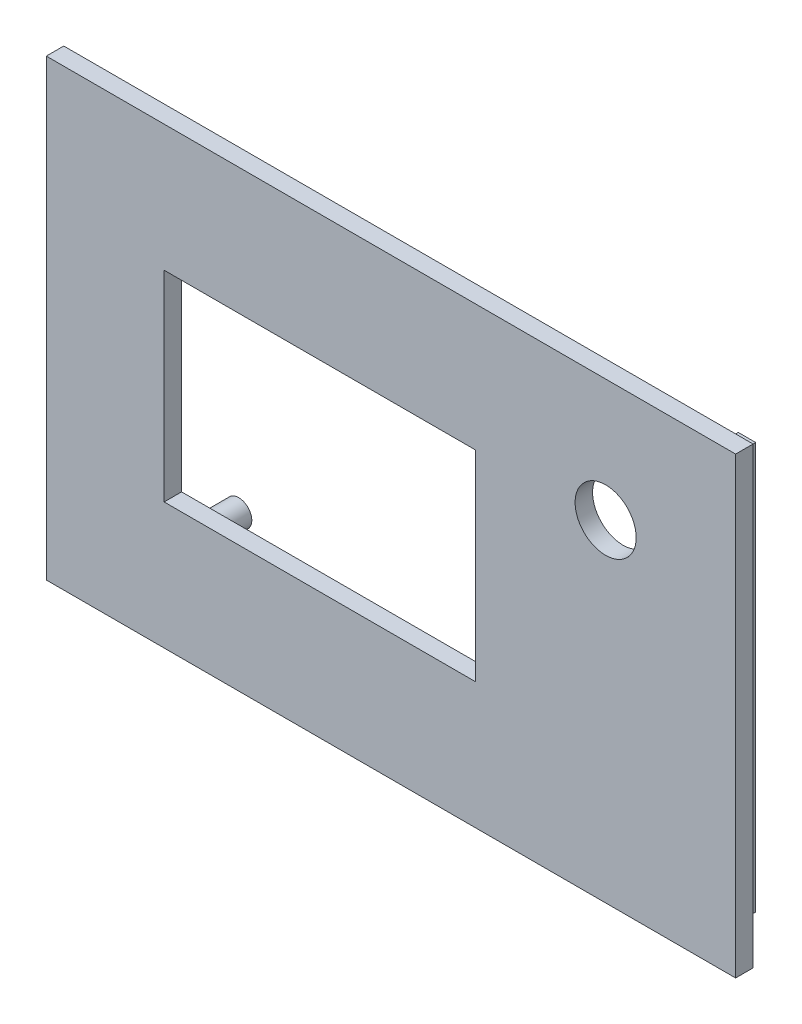
SolidWorks part; units mm, degrees
ref_plane "Ebene vorne" through (0, 0, 0) normal (0, 0, 1) x (1, 0, 0)
ref_plane "Ebene oben" through (0, 0, 0) normal (0, 1, 0) x (1, 0, 0)
ref_plane "Ebene rechts" through (0, 0, 0) normal (1, 0, 0) x (0, 0, -1)
sketch "Skizze10" plane through (0, 0, 0) normal (0, 0, 1) x (1, 0, 0)
  line L1 (-59.4904, -2.4023) -> (19.5096, -2.4023)
  line L2 (-59.4904, -2.4023) -> (-59.4904, -54.4023)
  line L3 (-59.4904, -54.4023) -> (19.5096, -54.4023)
  line L4 (19.5096, -2.4023) -> (19.5096, -54.4023)
  dimension "D1" = 79
  dimension "D2" = 52
extrude "Aufsatz-Linear austragen8" add sketch "Skizze10" along normal blind 2
sketch "Skizze11" plane through (0, 0, 2) normal (0, 0, 1) x (1, 0, 0)
  line L0 (-53.3332, -28.4023) -> (19.5096, -28.4023) construction
  line L1 (-45.987, -16.9023) -> (-10.287, -16.9023)
  line L2 (-45.987, -16.9023) -> (-45.987, -39.9023)
  line L3 (-45.987, -39.9023) -> (-10.287, -39.9023)
  line L4 (-10.287, -16.9023) -> (-10.287, -39.9023)
  line L5 (19.5096, -54.4023) -> (19.5096, -2.4023) construction
  dimension "D1" = 35.7
  dimension "D2" = 23
extrude "Schnitt-Linear austragen3" cut sketch "Skizze11" against normal blind 2
sketch "Skizze13" plane through (0, 0, 2) normal (0, 0, 1) x (1, 0, 0)
  line L0 (4.6113, 9.8264) -> (4.6113, -44.9541) construction
  line L2 (19.5096, -2.4023) -> (-59.4904, -2.4023) construction
  line L3 (19.5096, -54.4023) -> (19.5096, -2.4023) construction
  line L4 (-10.287, -39.9023) -> (-10.287, -16.9023) construction
  circle A0 centre (4.6113, -16.4023) radius 3.5
  dimension "D1" = 7
  dimension "D3" = 14
extrude "Schnitt-Linear austragen4" cut sketch "Skizze13" against normal blind 2 contours A0
sketch "Skizze14" plane through (0, 0, 0) normal (0, 0, -1) x (-1, 0, 0)
  line L0 (43.437, -7.9679) -> (43.437, -51.5306) construction
  line L1 (4.6842, -14.1023) -> (47.1284, -14.1023) construction
  line L3 (12.837, -5.7609) -> (12.837, -48.8799) construction
  line L4 (2.5413, -42.7023) -> (53.5844, -42.7023) construction
  line L5 (28.137, -6.7951) -> (28.137, -49.377) construction
  line L6 (10.287, -39.9023) -> (10.287, -16.9023) construction
  line L7 (45.987, -16.9023) -> (45.987, -39.9023) construction
  line L8 (-10.215, -28.4023) -> (57.4151, -28.4023) construction
  line L9 (10.287, -16.9023) -> (45.987, -16.9023) construction
  line L10 (45.987, -39.9023) -> (10.287, -39.9023) construction
  circle A0 centre (43.437, -14.1023) radius 1.5
  circle A1 centre (43.437, -42.7023) radius 1.5
  circle A2 centre (12.837, -14.1023) radius 1.5
  circle A3 centre (12.837, -42.7023) radius 1.5
  point P26 (0, 0)
  dimension "D1" = 3
  dimension "D6" = 3
  dimension "D7" = 3
  dimension "D8" = 3
  dimension "D2" = 30.6
  dimension "D3" = 28.6
extrude "Aufsatz-Linear austragen9" add sketch "Skizze14" along normal blind 4
sketch "Skizze15" plane through (0, 0, 0) normal (0, 0, -1) x (-1, 0, 0)
  line L0 (-16.8096, -5.1023) -> (-16.8096, -51.7023)
  line L1 (-16.8096, -51.7023) -> (56.7904, -51.7023)
  line L4 (59.4904, -54.4023) -> (59.4904, -2.4023)
  line L5 (59.4904, -2.4023) -> (-19.5096, -2.4023)
  line L6 (-19.5096, -2.4023) -> (-19.5096, -54.4023)
  line L7 (-19.5096, -54.4023) -> (59.4904, -54.4023)
  line L10 (-19.5096, -2.4023) -> (-19.5096, -54.4023) construction
  line L11 (-19.5096, -54.4023) -> (59.4904, -54.4023) construction
  line L12 (56.7904, -5.1023) -> (-16.8096, -5.1023) construction
  line L13 (56.7904, -51.7023) -> (56.7904, -5.1023) construction
  line L14 (59.4904, -54.4023) -> (59.4904, -2.4023) construction
  line L15 (59.4904, -2.4023) -> (-19.5096, -2.4023) construction
  line L16 (-14.8096, -5.1023) -> (-14.8096, -49.7023)
  line L17 (-14.8096, -49.7023) -> (56.7904, -49.7023)
  line L18 (-16.8096, -5.1023) -> (-14.8096, -5.1023)
  line L19 (56.7904, -51.7023) -> (56.7904, -49.7023)
  dimension "D1" = 0
  dimension "D2" = 2.7
  dimension "D3" = 2
extrude "Aufsatz-Linear austragen10" add sketch "Skizze15" along normal blind 3
